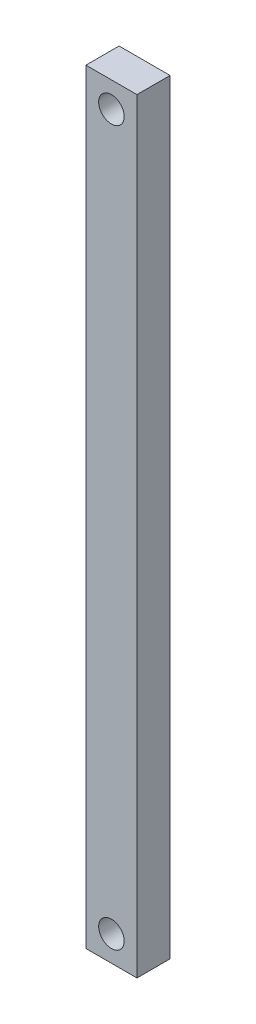
SolidWorks part; units mm, degrees
ref_plane "前视基准面" through (0, 0, 0) normal (0, 0, 1) x (1, 0, 0)
ref_plane "上视基准面" through (0, 0, 0) normal (0, 1, 0) x (1, 0, 0)
ref_plane "右视基准面" through (0, 0, 0) normal (1, 0, 0) x (0, 0, -1)
sketch "草图1" plane through (0, 0, 0) normal (0, 0, 1) x (1, 0, 0)
  line L0 (-13.886, 27.9365) -> (-3.886, 27.9365)
  line L1 (-3.886, 27.9365) -> (-3.886, -122.0635)
  line L2 (-3.886, -122.0635) -> (-13.886, -122.0635)
  line L3 (-13.886, -122.0635) -> (-13.886, 27.9365)
  line L4 (-8.886, 27.9365) -> (-8.886, 22.9365) construction
  line L5 (-8.886, -122.0635) -> (-8.886, -117.0635) construction
  circle A0 centre (-8.886, 22.9365) radius 2.5
  circle A1 centre (-8.886, -117.0635) radius 2.5
  dimension "D4" = 5
  dimension "D6" = 5
  dimension "D1" = 10
  dimension "D2" = 150
  dimension "D3" = 5
  dimension "D5" = 5
extrude "凸台-拉伸1" add sketch "草图1" along normal blind 6.5
